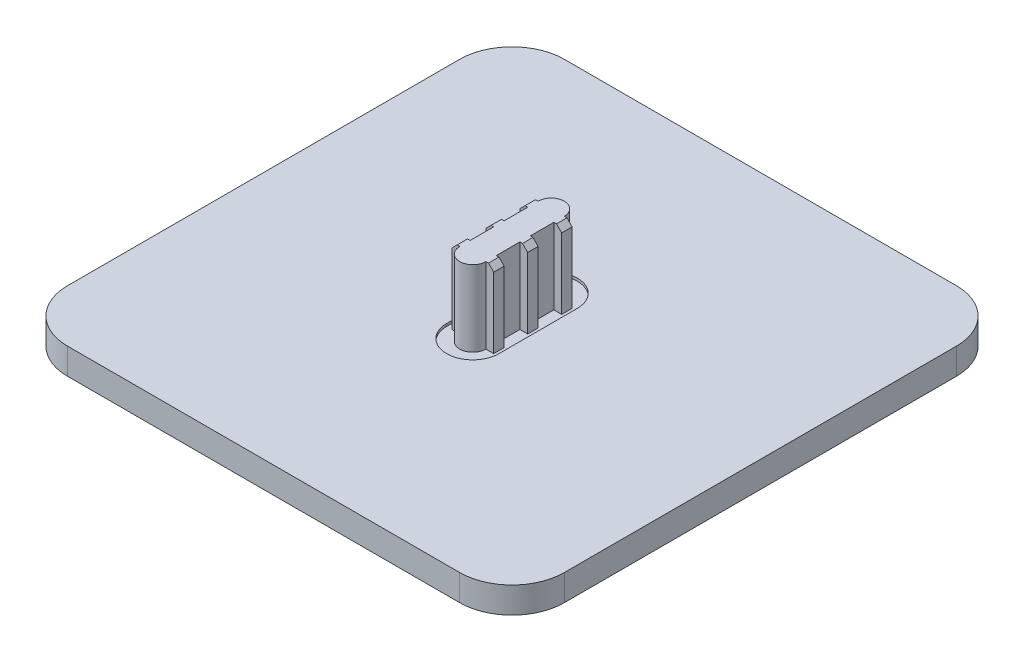
SolidWorks part; units mm, degrees
ref_plane "Front" through (0, 0, 0) normal (0, 0, 1) x (1, 0, 0)
ref_plane "Top" through (0, 0, 0) normal (0, 1, 0) x (1, 0, 0)
ref_plane "Right" through (0, 0, 0) normal (1, 0, 0) x (0, 0, -1)
sketch "Sketch1" plane through (0, 0, 0) normal (0, 1, 0) x (1, 0, 0)
  line L0 (10, 0) -> (85, 0)
  line L1 (95, 10) -> (95, 85)
  line L2 (0, 10) -> (0, 85)
  line L3 (10, 95) -> (85, 95)
  arc A0 (0, 10) -> (10, 0) centre (10, 10) ccw
  arc A1 (85, 0) -> (95, 10) centre (85, 10) ccw
  arc A2 (95, 85) -> (85, 95) centre (85, 85) ccw
  arc A3 (10, 95) -> (0, 85) centre (10, 85) ccw
  dimension "D1" = 95
  dimension "D2" = 95
extrude "Boss-Extrude1" add sketch "Sketch1" along normal blind 5
sketch "Sketch4" plane through (0, 5, 0) normal (0, 1, 0) x (1, 0, 0)
  line L1 (52.5, 55) -> (52.5, 40)
  line L3 (42.5, 40) -> (42.5, 55)
  arc A0 (42.5, 40) -> (52.5, 40) centre (47.5, 40) ccw
  arc A1 (52.5, 55) -> (42.5, 55) centre (47.5, 55) ccw
  dimension "D1" = 10
  dimension "D3" = 15
extrude "Cut-Extrude1" cut sketch "Sketch4" against normal blind 0.5
sketch "Sketch3" plane through (0, 5, 0) normal (0, 1, 0) x (1, 0, 0)
  line L0 (45, 53.0025) -> (45, 48.5025)
  line L2 (50, 53.0025) -> (50, 48.5025)
  line L4 (43.5, 46.5025) -> (45, 46.5025)
  line L5 (95, 10) -> (95, 85) construction
  line L6 (45, 55.0025) -> (43.5, 55.0025)
  line L7 (43.5, 55.0025) -> (43.5, 53.0025)
  line L8 (43.5, 53.0025) -> (45, 53.0025)
  line L9 (45, 46.5025) -> (45, 42.0025)
  line L10 (45, 40.0025) -> (43.5, 40.0025)
  line L11 (43.5, 40.0025) -> (43.5, 42.0025)
  line L12 (43.5, 42.0025) -> (45, 42.0025)
  line L13 (45, 48.5025) -> (43.5, 48.5025)
  line L14 (43.5, 48.5025) -> (43.5, 46.5025)
  line L15 (50, 55.0025) -> (51.5, 55.0025)
  line L16 (51.5, 48.5025) -> (51.5, 46.5025)
  line L17 (50, 48.5025) -> (51.5, 48.5025)
  line L18 (51.5, 42.0025) -> (50, 42.0025)
  line L19 (51.5, 40.0025) -> (51.5, 42.0025)
  line L20 (50, 40.0025) -> (51.5, 40.0025)
  line L21 (51.5, 53.0025) -> (50, 53.0025)
  line L22 (51.5, 55.0025) -> (51.5, 53.0025)
  line L23 (51.5, 46.5025) -> (50, 46.5025)
  line L24 (50, 46.5025) -> (50, 42.0025)
  arc A0 (50, 55.0025) -> (45, 55.0025) centre (47.5, 55.0025) ccw
  arc A1 (45, 40.0025) -> (50, 40.0025) centre (47.5, 40.0025) ccw
  dimension "D3" = 2
  dimension "D1" = 4.5
  dimension "D2" = 5
  dimension "D4" = 45
extrude "Boss-Extrude2" add sketch "Sketch3" along normal blind 14 and the other way through all
chamfer "Chamfer2" distance 1 angle 45 6 edges at (43.5, 19, -47.5025) (43.5, 19, -54.0025) (51.5, 19, -54.0025) (51.5, 19, -47.5025) (51.5, 19, -41.0025) (43.5, 19, -41.0025)
